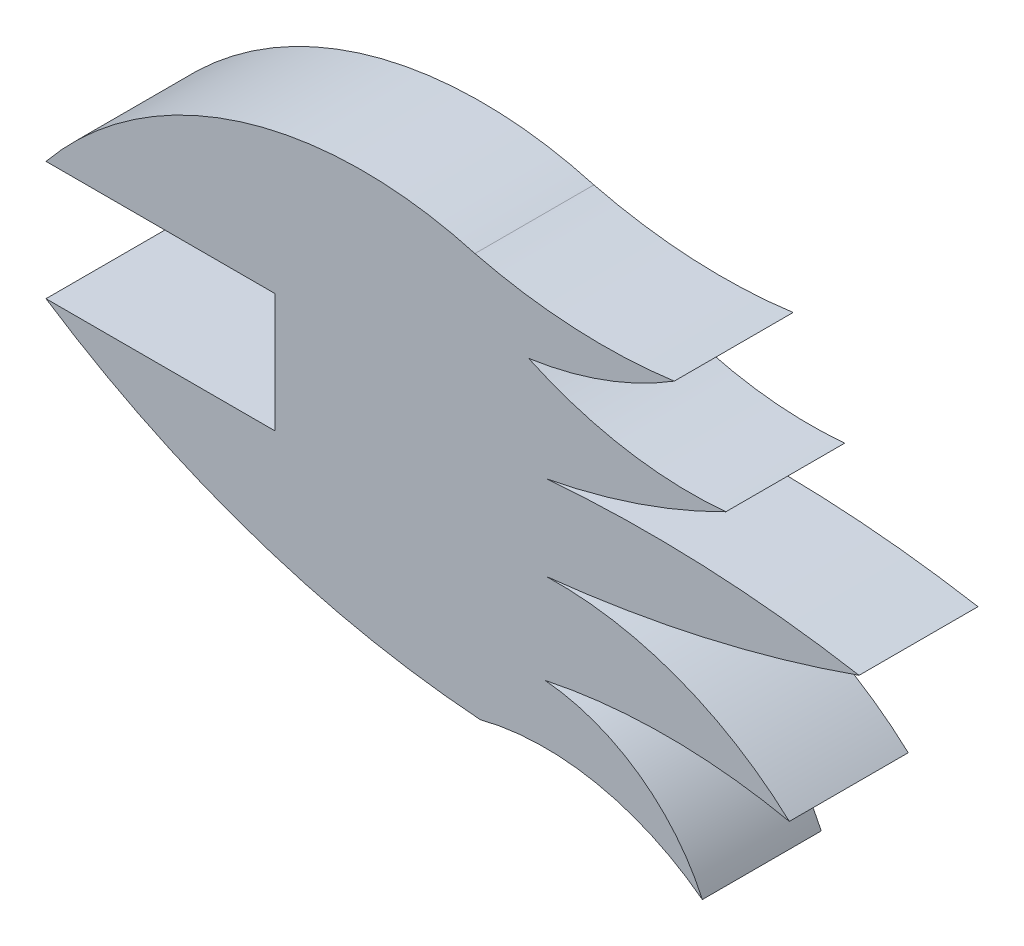
SolidWorks part; units mm, degrees
ref_plane "Front Plane" through (0, 0, 0) normal (0, 0, 1) x (1, 0, 0)
ref_plane "Top Plane" through (0, 0, 0) normal (0, 1, 0) x (1, 0, 0)
ref_plane "Right Plane" through (0, 0, 0) normal (1, 0, 0) x (0, 0, -1)
sketch "Sketch1" plane through (0, 0, 0) normal (0, 0, 1) x (1, 0, 0)
  line L0 (23.6997, 1.524) -> (23.6997, 0)
  line L1 (23.6997, 0) -> (20.7676, 0)
  line L3 (20.7676, 1.524) -> (23.6997, 1.524)
  arc A0 (20.7676, 0) -> (26.3329, -1.89) centre (27.1776, 9.736) ccw
  arc A1 (26.3329, -1.89) -> (29.1798, -2.4636) centre (27.1632, -5.121) cw
  arc A2 (29.1798, -2.4636) -> (27.1632, -1.0384) centre (26.9523, -3.4762) ccw
  arc A3 (27.1632, -1.0384) -> (30.2946, -1.0384) centre (28.7289, -8.4607) cw
  arc A4 (30.2946, -1.0384) -> (27.1776, 0.1231) centre (27.3014, -4.3078) ccw
  arc A5 (27.1776, 0.1231) -> (31.1887, 1.0301) centre (25.3175, 17.6726) ccw
  arc A6 (31.1887, 1.0301) -> (27.1776, 1.2079) centre (28.4934, -14.4407) ccw
  arc A7 (27.1776, 1.2079) -> (29.481, 1.9915) centre (25.5815, 9.6767) ccw
  arc A8 (29.481, 1.9915) -> (26.9523, 2.4307) centre (29.0333, 6.9133) cw
  arc A9 (26.9523, 2.4307) -> (28.8195, 3.1108) centre (26.2656, 7.2187) ccw
  arc A10 (28.8195, 3.1108) -> (26.2656, 3.2498) centre (27.9059, 9.8547) cw
  arc A11 (26.2656, 3.2498) -> (20.7676, 1.524) centre (24.8293, -1.7951) ccw
extrude "Boss-Extrude1" add sketch "Sketch1" along normal blind 1.524
